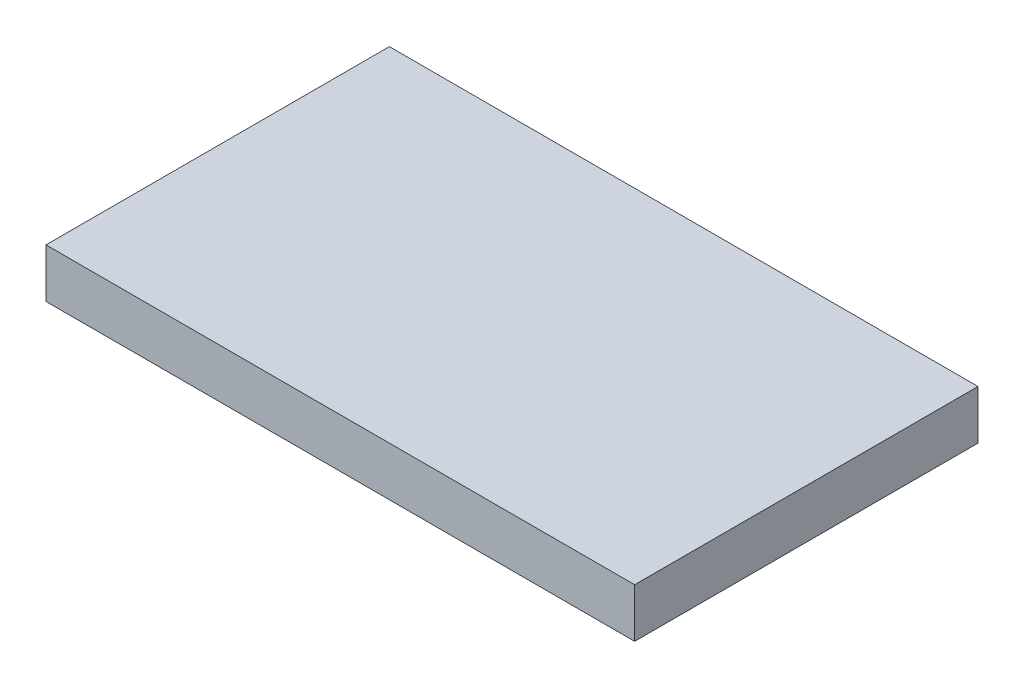
SolidWorks part; units mm, degrees
ref_plane "Front Plane" through (0, 0, 0) normal (0, 0, 1) x (1, 0, 0)
ref_plane "Top Plane" through (0, 0, 0) normal (0, 1, 0) x (1, 0, 0)
ref_plane "Right Plane" through (0, 0, 0) normal (1, 0, 0) x (0, 0, -1)
sketch "Sketch1" plane through (0, 0, 0) normal (0, 1, 0) x (1, 0, 0)
  line L1 (0, 0) -> (304.8, 0)
  line L2 (0, 0) -> (0, 177.8)
  line L3 (0, 177.8) -> (304.8, 177.8)
  line L4 (304.8, 0) -> (304.8, 177.8)
  dimension "D1" = 177.8
  dimension "D2" = 304.8
extrude "Boss-Extrude1" add sketch "Sketch1" along normal blind 25.4
